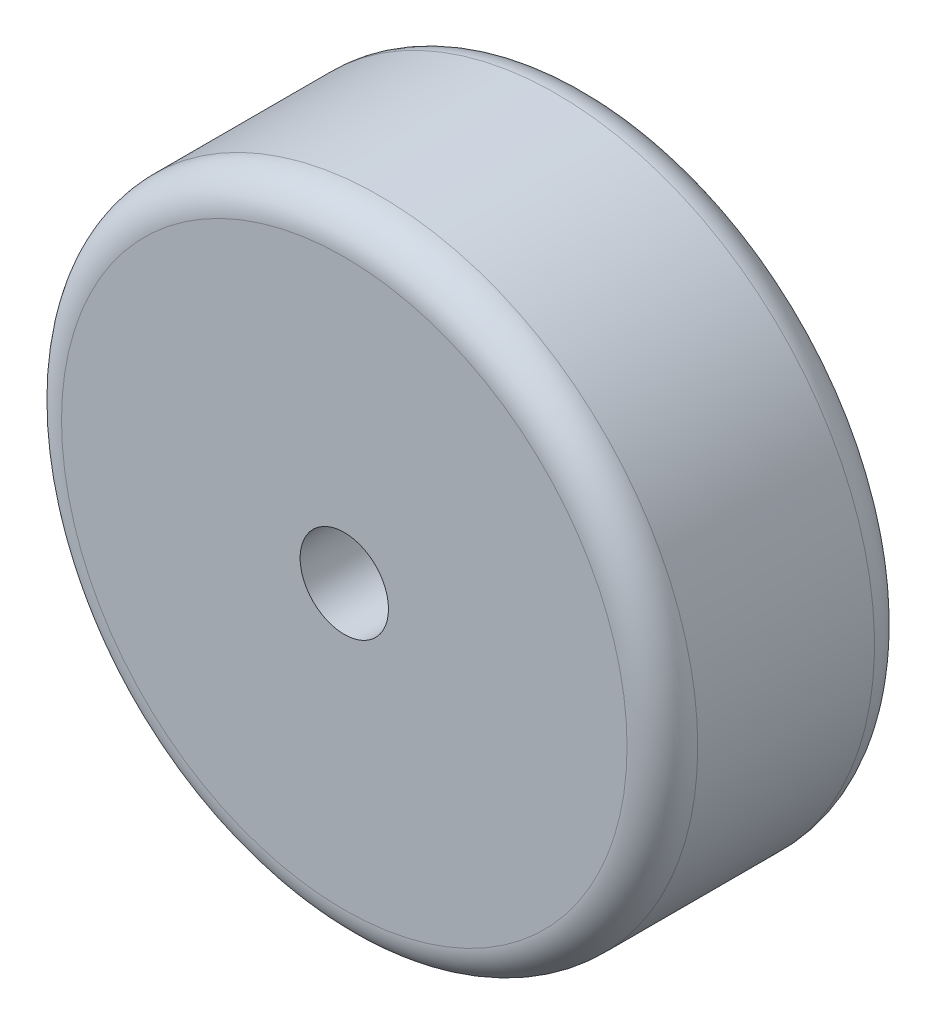
SolidWorks part; units mm, degrees
ref_plane "Front Plane" through (0, 0, 0) normal (0, 0, 1) x (1, 0, 0)
ref_plane "Top Plane" through (0, 0, 0) normal (0, 1, 0) x (1, 0, 0)
ref_plane "Right Plane" through (0, 0, 0) normal (1, 0, 0) x (0, 0, -1)
sketch "Sketch1" plane through (0, 0, 0) normal (0, 0, 1) x (1, 0, 0)
  circle A0 centre (0, 0) radius 18
  dimension "D1" = 36
extrude "Boss-Extrude1" add sketch "Sketch1" along normal blind 7
mirror "Mirror1" about plane through (0, 0, 0) normal (0, 0, 1) of "Boss-Extrude1"
fillet "Fillet2" radius 2 2 edges at (18, 0, 7) (18, 0, -7)
sketch "Sketch2" plane through (0, 0, 7) normal (0, 0, 1) x (1, 0, 0)
  line L0 (-16, 0) -> (16, 0) construction
  circle A0 centre (0, 0) radius 16 construction
  circle A1 centre (0, 0) radius 2.5
  dimension "D1" = 5
extrude "Cut-Extrude1" cut sketch "Sketch2" against normal up to next
